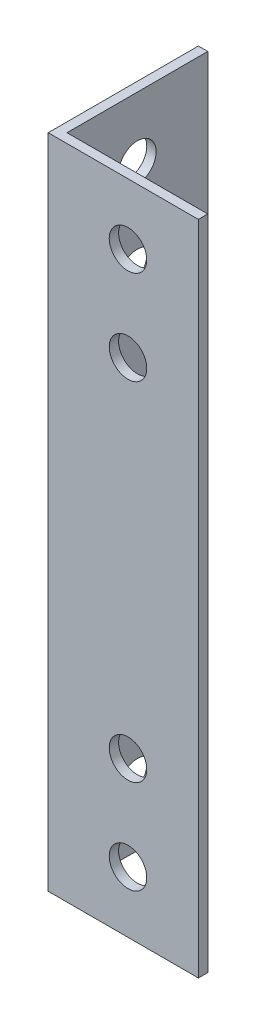
SolidWorks part; units mm, degrees
ref_plane "Face" through (0, 0, 0) normal (0, 0, 1) x (1, 0, 0)
ref_plane "Dessus" through (0, 0, 0) normal (0, 1, 0) x (1, 0, 0)
ref_plane "Droite" through (0, 0, 0) normal (1, 0, 0) x (0, 0, -1)
sketch "Esquisse1" plane through (0, 0, 0) normal (0, 1, 0) x (1, 0, 0)
  line L0 (0, 0) -> (0, 16)
  line L1 (0, 16) -> (1, 16)
  line L2 (1, 16) -> (1, 1)
  line L3 (1, 1) -> (16, 1)
  line L4 (16, 1) -> (16, 0)
  line L5 (16, 0) -> (0, 0)
  dimension "D1" = 1
  dimension "D2" = 1
  dimension "D3" = 90
  dimension "D4" = 15
extrude "Extrusion1" add sketch "Esquisse1" along normal blind 70
sketch "Esquisse2" plane through (1, 0, 0) normal (1, 0, 0) x (0, 0, -1)
  line L0 (1, 35) -> (16, 35) construction
  line L1 (1, 70) -> (1, 0) construction
  line L2 (16, 70) -> (16, 0) construction
  line L3 (8.5, 0) -> (8.5, 70) construction
  line L4 (1, 0) -> (16, 0) construction
  line L5 (1, 70) -> (16, 70) construction
  circle A0 centre (8.5, 16.5) radius 2
  circle A1 centre (8.5, 6.5) radius 2
  circle A2 centre (8.5, 53.5) radius 2
  circle A3 centre (8.5, 63.5) radius 2
  dimension "D1" = 4
  dimension "D2" = 18.5
  dimension "D3" = 10
extrude "Extrusion2" cut sketch "Esquisse2" against normal up to next
sketch "Esquisse3" plane through (0, 0, -1) normal (0, 0, -1) x (-1, 0, 0)
  line L0 (-8.5, 70) -> (-8.5, 0) construction
  line L1 (-16, 70) -> (-1, 70) construction
  line L2 (-16, 0) -> (-1, 0) construction
  line L3 (-16, 35) -> (-1, 35) construction
  line L4 (-16, 70) -> (-16, 0) construction
  line L5 (-1, 70) -> (-1, 0) construction
  circle A0 centre (-8.5, 53.5) radius 2
  circle A1 centre (-8.5, 63.5) radius 2
  circle A2 centre (-8.5, 6.5) radius 2
  circle A3 centre (-8.5, 16.5) radius 2
  dimension "D1" = 4
  dimension "D2" = 18.5
  dimension "D3" = 10
extrude "Extrusion3" cut sketch "Esquisse3" against normal up to next
